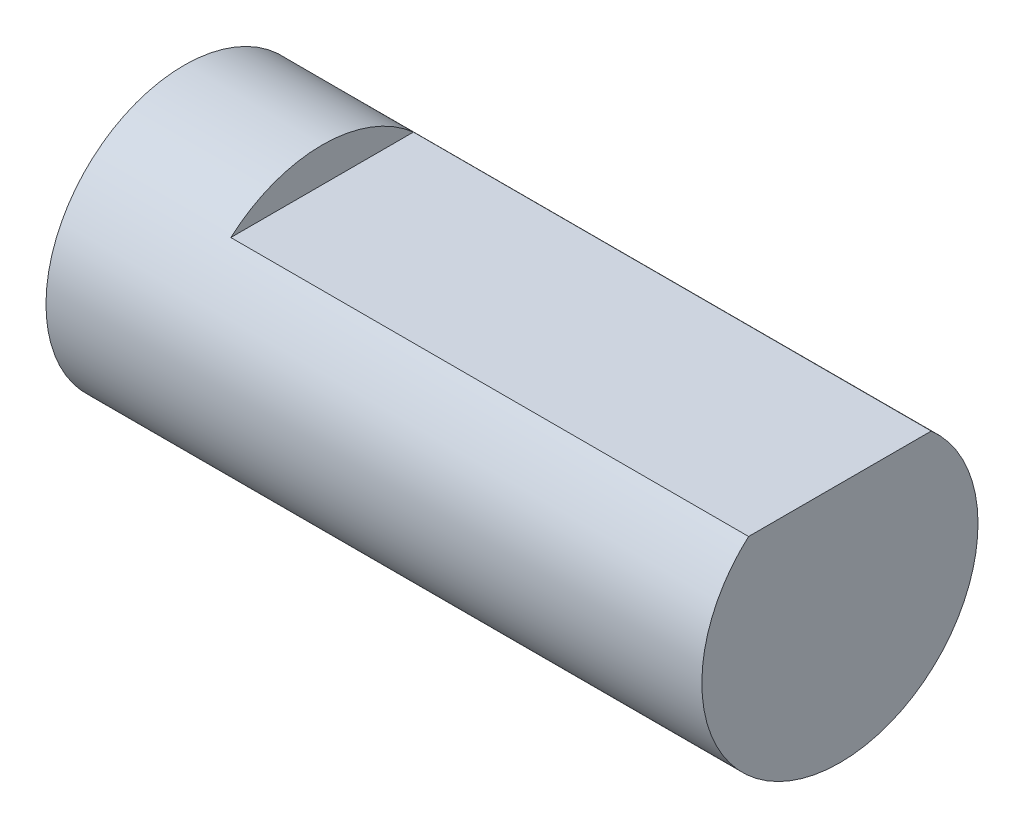
SolidWorks part; units mm, degrees
ref_plane "Piano frontale" through (0, 0, 0) normal (0, 0, 1) x (1, 0, 0)
ref_plane "Piano superiore" through (0, 0, 0) normal (0, 1, 0) x (1, 0, 0)
ref_plane "Piano destro" through (0, 0, 0) normal (1, 0, 0) x (0, 0, -1)
sketch "Schizzo1" plane through (0, 0, 0) normal (1, 0, 0) x (0, 0, -1)
  circle A0 centre (0, 0) radius 4
  dimension "D1" = 8
extrude "Estrusione-Estrusione1" add sketch "Schizzo1" along normal blind 19
sketch "Schizzo2" plane through (19, 0, 0) normal (1, 0, 0) x (0, 0, -1)
  line L0 (-2.6458, 3) -> (2.6458, 3)
  circle A0 centre (0, 0) radius 4 construction
  circle A1 centre (0, 0) radius 4
  circle M3 centre (0, 0) radius 4
  dimension "D1" = 3
extrude "Taglio-Estrusione1" cut sketch "Schizzo2" against normal blind 15 contours L0 M3
